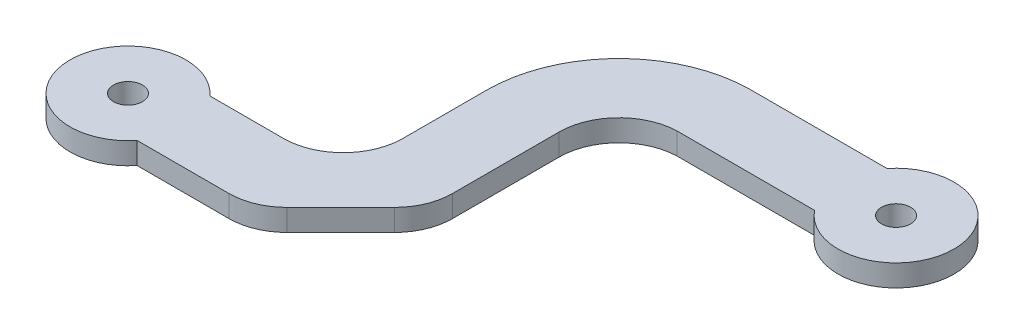
SolidWorks part; units mm, degrees
ref_plane "Front Plane" through (0, 0, 0) normal (0, 0, 1) x (1, 0, 0)
ref_plane "Top Plane" through (0, 0, 0) normal (0, 1, 0) x (1, 0, 0)
ref_plane "Right Plane" through (0, 0, 0) normal (1, 0, 0) x (0, 0, -1)
sketch "Sketch1" plane through (0, 0, 0) normal (0, 1, 0) x (1, 0, 0)
  line L0 (0, 0) -> (4, 0) construction
  line L5 (3.1225, -2.5) -> (11.1225, -2.5)
  line L6 (2.9783, 2.6702) -> (8.0553, 2.6702)
  line L8 (11.1225, -2.5) -> (17.1753, 3.5528)
  line L11 (17.1753, 3.5528) -> (17.1753, 12.5528)
  line L18 (21.1654, 21.6884) -> (30.6654, 21.6884)
  line L20 (12.1753, 12.5528) -> (12.1753, 6.7902)
  line L27 (17.1753, 12.5528) -> (12.1753, 12.5528)
  line L28 (21.1654, 16.6884) -> (30.6654, 16.6884)
  line L29 (30.6654, 19.1884) -> (30.6654, 16.6884) construction
  arc A0 (2.9783, 2.6702) -> (3.1225, -2.5) centre (0, 0) ccw
  arc A2 (8.0553, 2.6702) -> (12.1753, 6.7902) centre (8.0553, 6.7902) ccw
  arc A3 (17.1753, 12.5528) -> (21.1654, 16.6884) centre (21.3136, 12.5528) cw
  arc A4 (12.1753, 12.5528) -> (21.1654, 21.6884) centre (21.3121, 12.5528) cw
  arc A5 (30.6654, 16.6884) -> (30.6654, 21.6884) centre (33.7879, 19.1884) ccw
  point P7 (0, 0)
  dimension "D1" = 8
  dimension "D6" = 9.5
  dimension "D2" = 9
  dimension "D3" = 8
  dimension "D4" = 8.56
  dimension "D5" = 45
  dimension "D7" = 5
  dimension "D8" = 5
  dimension "D9" = 4
  dimension "D10" = 4
  dimension "D11" = 33.7879
extrude "Boss-Extrude1" add sketch "Sketch1" along normal blind 1.5 contours L28 A5 L18 A4 L27 A3 | A2 L6 A0 L5 L8 L11 L27 L20
fillet "Fillet1" radius 4 2 edges at (17.1753, 0.75, -3.5528) (11.1225, 0.75, 2.5)
sketch "Sketch2" plane through (0, 1.5, 0) normal (0, 1, 0) x (1, 0, 0)
  circle A0 centre (0, 0) radius 1
  circle A1 centre (33.7879, 19.1884) radius 1
  dimension "D1" = 2
  dimension "D2" = 2
extrude "Cut-Extrude1" cut sketch "Sketch2" against normal blind 11.5
